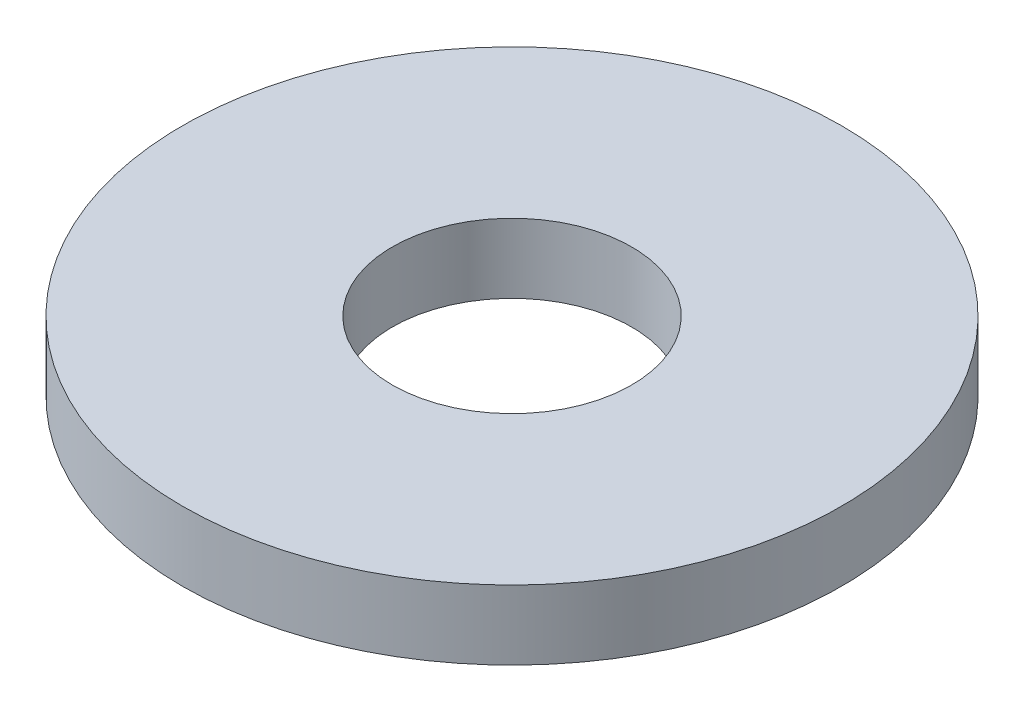
SolidWorks part; units mm, degrees
ref_plane "Plan de face" through (0, 0, 0) normal (0, 0, 1) x (1, 0, 0)
ref_plane "Plan de dessus" through (0, 0, 0) normal (0, 1, 0) x (1, 0, 0)
ref_plane "Plan de droite" through (0, 0, 0) normal (1, 0, 0) x (0, 0, -1)
sketch "Esquisse1" plane through (0, 0, 0) normal (0, 1, 0) x (1, 0, 0)
  circle A0 centre (0, 0) radius 3.45
  circle A1 centre (0, 0) radius 9.5
  dimension "D1" = 6.9
  dimension "13.95" = 19
extrude "Boss.-Extru.1" add sketch "Esquisse1" along normal blind 2
